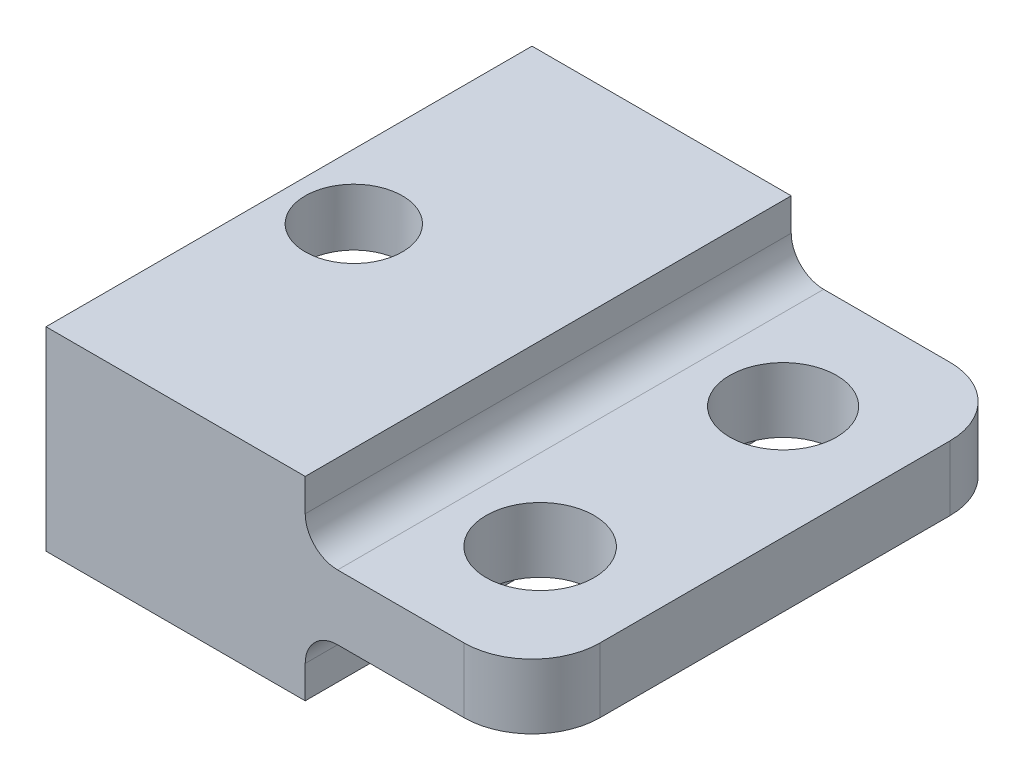
SolidWorks part; units mm, degrees
ref_plane "Front Plane" through (0, 0, 0) normal (0, 0, 1) x (1, 0, 0)
ref_plane "Top Plane" through (0, 0, 0) normal (0, 1, 0) x (1, 0, 0)
ref_plane "Right Plane" through (0, 0, 0) normal (1, 0, 0) x (0, 0, -1)
sketch "Sketch1" plane through (0, 0, 0) normal (0, 1, 0) x (1, 0, 0)
  line L1 (0, 0) -> (-7, 0)
  line L2 (0, 0) -> (0, 15)
  line L3 (0, 15) -> (-7, 15)
  line L4 (-7, 0) -> (-7, 15)
  line L5 (0, 15) -> (8, 15)
  line L6 (0, 15) -> (0, 0)
  line L7 (0, 0) -> (8, 0)
  line L8 (8, 15) -> (8, 0)
  dimension "D1" = 15
  dimension "D2" = 7
  dimension "D3" = 8
extrude "Boss-Extrude1" add sketch "Sketch1" along normal blind 2 contours L4 L1 L2 L3 | L8 L5 L2 L7
sketch "Sketch2" plane through (0, 0, 0) normal (0, -1, 0) x (1, 0, 0)
  line L1 (-7, 0) -> (1, 0)
  line L2 (8, 0) -> (-7, 0) construction
  line L3 (1, 0) -> (1, -15)
  line L4 (8, -15) -> (-7, -15) construction
  line L6 (1, 0) -> (-7, 0)
  line L7 (1, 0) -> (1, -15)
  line L8 (1, -15) -> (-7, -15)
  line L9 (-7, 0) -> (-7, -15)
  dimension "D1" = 8
extrude "Boss-Extrude2" add sketch "Sketch2" along normal blind 2 contours L7 L6 L9 L8
sketch "Sketch3" plane through (0, 2, 0) normal (0, 1, 0) x (1, 0, 0)
  line L0 (8, 0) -> (-7, 0) construction
  line L1 (-7, 15) -> (1, 15)
  line L2 (-7, 15) -> (-7, 0)
  line L3 (-7, 0) -> (1, 0)
  line L4 (1, 15) -> (1, 0)
  dimension "D1" = 8
extrude "Boss-Extrude4" add sketch "Sketch3" along normal blind 2
sketch "Sketch4" plane through (0, 0, 0) normal (0, -1, 0) x (-1, 0, 0)
  line L0 (-1, 0) -> (-1, 15) construction
  line L1 (-8, 0) -> (-1, 0)
  line L2 (-8, 0) -> (-8, 7.5)
  line L4 (-1, 0) -> (-1, 7.5)
  circle A0 centre (-4.5, 3.75) radius 1.665
  circle A1 centre (-4.5, 11.25) radius 1.65
extrude "Cut-Extrude1" cut sketch "Sketch4" against normal blind 9 contours A0 | A1
fillet "Fillet1" radius 2.1 1 edges at (8, 1, 0)
fillet "Fillet2" radius 2.1 1 edges at (8, 1, -15)
sketch "Sketch5" plane through (-7, 0, 0) normal (-1, 0, 0) x (0, 0, 1)
  line L0 (-15, -2) -> (-15, -0.7632)
  line L1 (-15, 4) -> (-15, -2) construction
  line L2 (-15, -0.7632) -> (-15, 2.2368)
  line L3 (0, 4) -> (0, -2) construction
  line L4 (-15, -0.7632) -> (0, -0.7632)
  line L5 (-15, -0.7632) -> (-15, 2.2368)
  line L6 (-15, 2.2368) -> (0, 2.2368)
  line L7 (0, -0.7632) -> (0, 2.2368)
  line L9 (0, 2.2368) -> (-1.5, 2.2368)
  line L10 (0, 2.2368) -> (0, -0.7632)
  line L11 (0, -0.7632) -> (-1.5, -0.7632)
  line L12 (-1.5, 2.2368) -> (-1.5, -0.7632)
  line L13 (-15, -0.7632) -> (-13.5, -0.7632)
  line L14 (-15, -0.7632) -> (-15, 2.2368)
  line L15 (-15, 2.2368) -> (-13.5, 2.2368)
  line L16 (-13.5, -0.7632) -> (-13.5, 2.2368)
  line L17 (-13.5, -0.7632) -> (-1.5, -0.7632)
  line L18 (-13.5, -0.7632) -> (-13.5, 2.2368)
  line L19 (-13.5, 2.2368) -> (-1.5, 2.2368)
  line L20 (-1.5, -0.7632) -> (-1.5, 2.2368)
  dimension "D1" = 3
  dimension "D2" = 1.5
  dimension "D3" = 1.5
extrude "Cut-Extrude2" cut sketch "Sketch5" against normal blind 3.8 contours L16 L4 L12 L6
sketch "Sketch6" plane through (0, 4, 0) normal (0, 1, 0) x (1, 0, 0)
  line L0 (1, 15) -> (-7, 15) construction
  line L1 (-7, 0) -> (-3, 0)
  line L2 (-7, 0) -> (-7, 15)
  line L3 (-7, 15) -> (-3, 15)
  line L4 (-3, 0) -> (-3, 15)
  circle A0 centre (-5, 7.5) radius 1.5
  dimension "D1" = 4
extrude "Cut-Extrude3" cut sketch "Sketch6" against normal blind 17.2 contours A0
fillet "Fillet3" radius 1 1 edges at (1, 0, -7.5)
fillet "Fillet4" radius 1 1 edges at (1, 2, -7.5)
sketch "Sketch7" plane through (-3.2, 0, 0) normal (-1, 0, 0) x (0, 0, 1)
  line L1 (-13.5, -0.7632) -> (-1.5, -0.7632)
  line L2 (-13.5, -0.7632) -> (-13.5, 2.2368)
  line L3 (-13.5, 2.2368) -> (-1.5, 2.2368)
  line L4 (-1.5, -0.7632) -> (-1.5, 2.2368)
extrude "Cut-Extrude4" cut sketch "Sketch7" against normal blind 0.2
